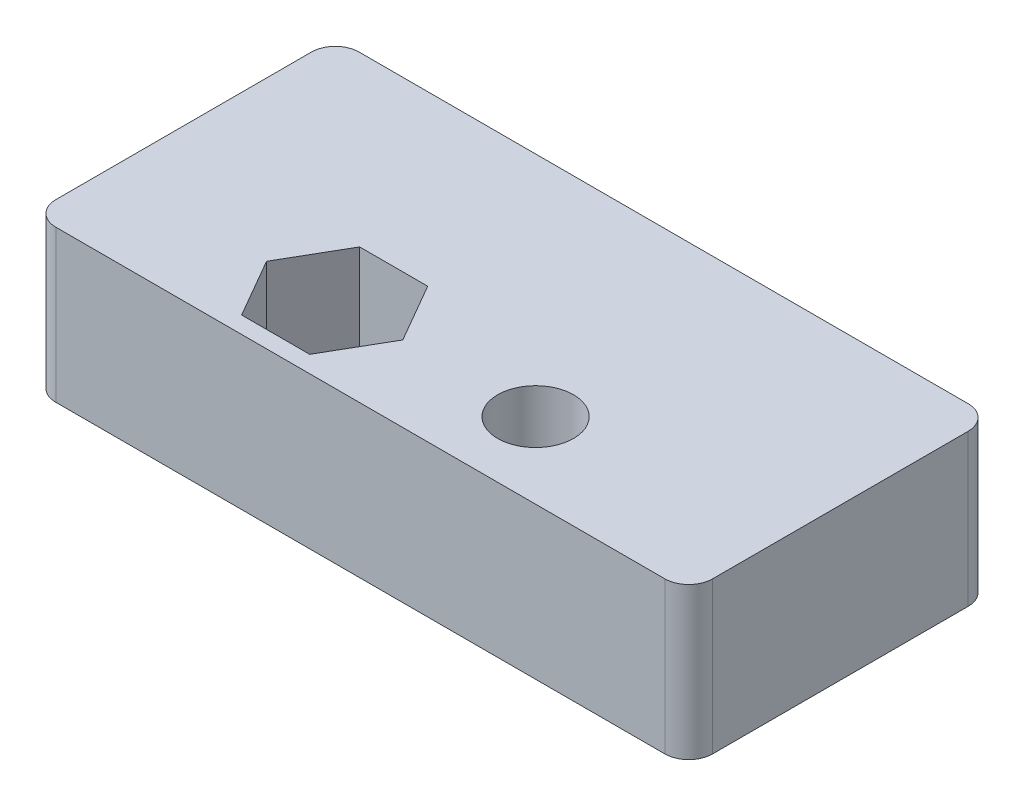
SolidWorks part; units mm, degrees
material "Balsa"
ref_plane "Front Plane" through (0, 0, 0) normal (0, 0, 1) x (1, 0, 0)
ref_plane "Top Plane" through (0, 0, 0) normal (0, 1, 0) x (1, 0, 0)
ref_plane "Right Plane" through (0, 0, 0) normal (1, 0, 0) x (0, 0, -1)
sketch "Sketch1" plane through (0, 0, 0) normal (0, 1, 0) x (1, 0, 0)
  line L1 (0, 0) -> (27.5, 0)
  line L2 (0, 0) -> (0, 12.7)
  line L3 (0, 12.7) -> (27.5, 12.7)
  line L4 (27.5, 0) -> (27.5, 12.7)
  line L5 (12.3523, 3.175) -> (10.9261, 5.6452)
  line L6 (10.9261, 5.6452) -> (8.0739, 5.6452)
  line L7 (8.0739, 5.6452) -> (6.6477, 3.175)
  line L8 (6.6477, 3.175) -> (8.0739, 0.7049)
  line L9 (8.0739, 0.7049) -> (10.9261, 0.7048)
  line L10 (10.9261, 0.7048) -> (12.3523, 3.175)
  circle A0 centre (9.5, 3.175) radius 1.75 construction
  circle A1 centre (17.9125, 3.175) radius 1.5875
  circle A2 centre (9.5, 3.175) radius 2.4701 construction
  dimension "D3" = 3.175
  dimension "D4" = 3.5
  dimension "D1" = 27.5
  dimension "D2" = 12.7
  dimension "D5" = 9.5
  dimension "D6" = 3.175
  dimension "D7" = 3.175
  dimension "D8" = 8.4125
  dimension "D9" = 4.9403
extrude "Boss-Extrude1" add sketch "Sketch1" along normal blind 6.35
fillet "Fillet1" radius 1 4 edges at (0, 3.175, 0) (0, 3.175, -12.7) (27.5, 3.175, -12.7) (27.5, 3.175, 0)
other "Move Face1" [suppressed] parameters "D1"=0.08
